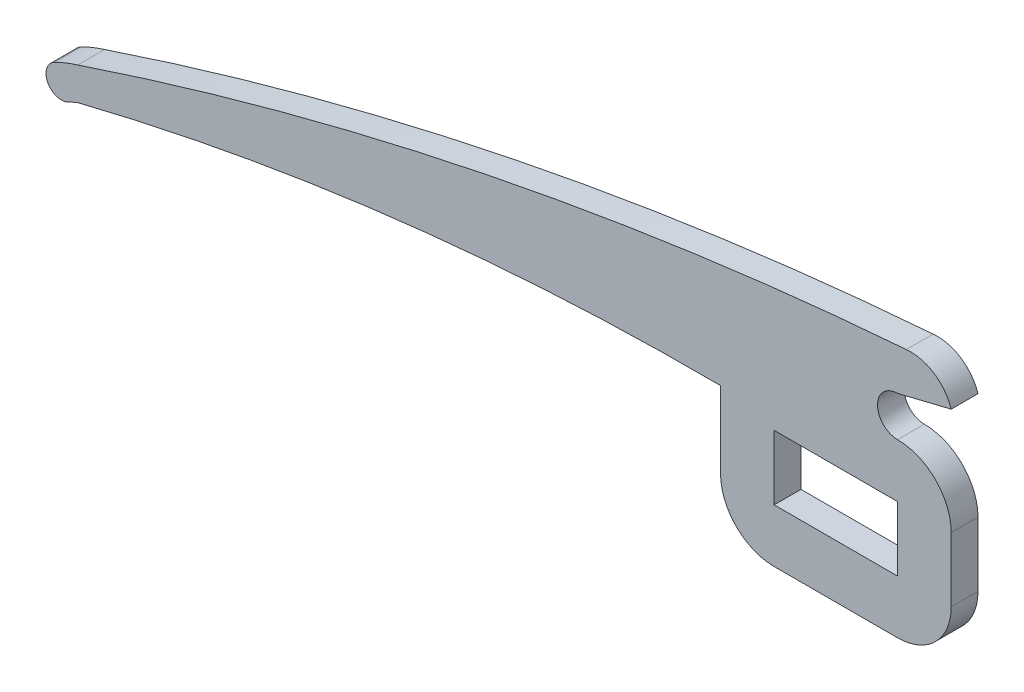
SolidWorks part; units mm, degrees
ref_plane "Front Plane" through (0, 0, 0) normal (0, 0, 1) x (1, 0, 0)
ref_plane "Top Plane" through (0, 0, 0) normal (0, 1, 0) x (1, 0, 0)
ref_plane "Right Plane" through (0, 0, 0) normal (1, 0, 0) x (0, 0, -1)
sketch "Sketch4" plane through (0, 0, 0) normal (0, 0, 1) x (1, 0, 0)
  line L0 (0, 0) -> (-23.0108, 0)
  line L1 (-23.0108, 0) -> (-23.0108, 12.0354)
  line L2 (-23.0108, 12.0354) -> (0, 12.0354)
  line L3 (0, 12.0354) -> (0, 0)
  line L4 (-23.0295, -9.9695) -> (0.0201, -9.9695)
  line L5 (-33.0178, 12.0354) -> (-33.0178, 0.0187)
  line L6 (-33.0178, 12.0354) -> (-33.0178, 14.2611)
  line L7 (10.0096, 12.0354) -> (10.0096, 0.02)
  line L9 (10.0096, 31.9659) -> (0.0023, 29.5135)
  arc A0 (10.0096, 0.02) -> (0.0201, -9.9695) centre (0.0201, 0.02) cw
  arc A1 (-23.0295, -9.9695) -> (-33.0178, 0.0187) centre (-23.0295, 0.0187) cw
  arc A2 (1.6315, 37.4137) -> (10.0096, 31.9659) centre (2.4547, 29.5135) cw
  arc A3 (0.0023, 22.0404) -> (10.0096, 12.0354) centre (0.0023, 12.0331) cw
  arc A5 (-152.9228, 0.0187) -> (-33.0178, 14.2611) centre (-36.4352, -468.8225) cw
  arc A6 (-152.9228, 6.1092) -> (-157.2654, 4.3613) centre (-144.8954, -20.1017) ccw
  arc A7 (-157.2654, 4.3613) -> (-154.6707, -0.7701) centre (-155.968, 1.7956) ccw
  arc A8 (-154.6707, -0.7701) -> (-152.9228, 0.0187) centre (-144.8882, -20.1161) cw
  arc A9 (0.0023, 29.5135) -> (0.0023, 22.0404) centre (0.0023, 25.777) ccw
  arc A10 (-152.9228, 6.1092) -> (1.6315, 37.4137) centre (50.6287, -601.6709) cw
  dimension "D1" = 23.0108
  dimension "D2" = 12.0354
  dimension "D3" = 122.9503
extrude "Boss-Extrude1" add sketch "Sketch4" along normal blind 5
